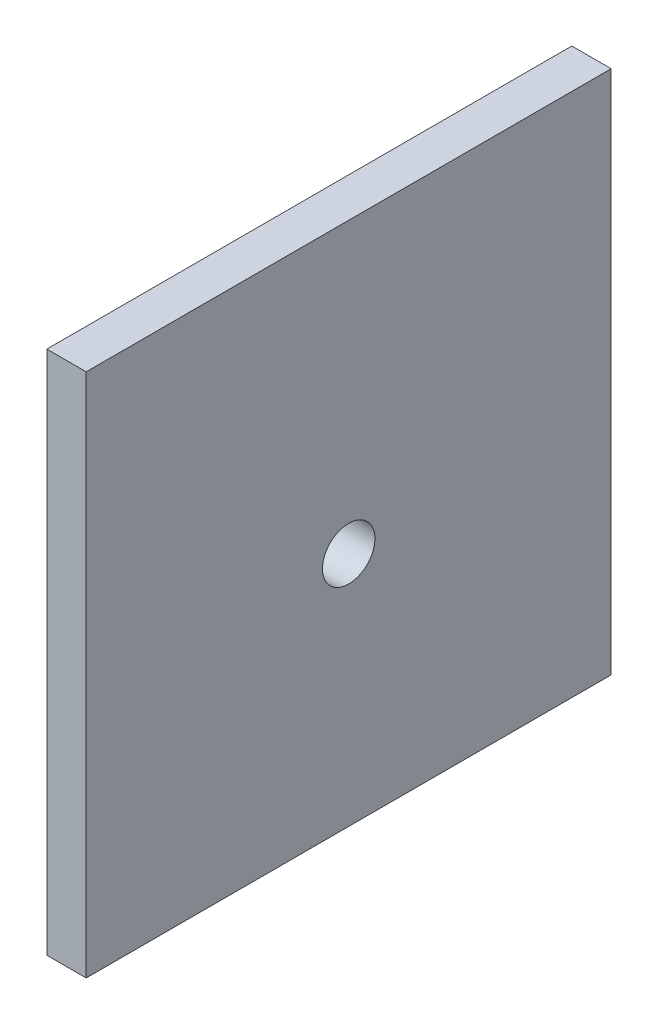
SolidWorks part; units mm, degrees
ref_plane "Alzado" through (0, 0, 0) normal (0, 0, 1) x (1, 0, 0)
ref_plane "Planta" through (0, 0, 0) normal (0, 1, 0) x (1, 0, 0)
ref_plane "Vista lateral" through (0, 0, 0) normal (1, 0, 0) x (0, 0, -1)
sketch "Croquis1" plane through (0, 0, 0) normal (1, 0, 0) x (0, 0, -1)
  line L0 (-31.2692, 7.8027) -> (8.7308, 7.8027)
  line L1 (8.7308, 7.8027) -> (8.7308, -32.1973)
  line L2 (8.7308, -32.1973) -> (-31.2692, -32.1973)
  line L3 (-31.2692, -32.1973) -> (-31.2692, 7.8027)
  circle A0 centre (-11.2692, -14.1973) radius 2
  dimension "D1" = 4
  dimension "D2" = 40
  dimension "D3" = 40
extrude "Saliente-Extruir1" add sketch "Croquis1" along normal blind 3
